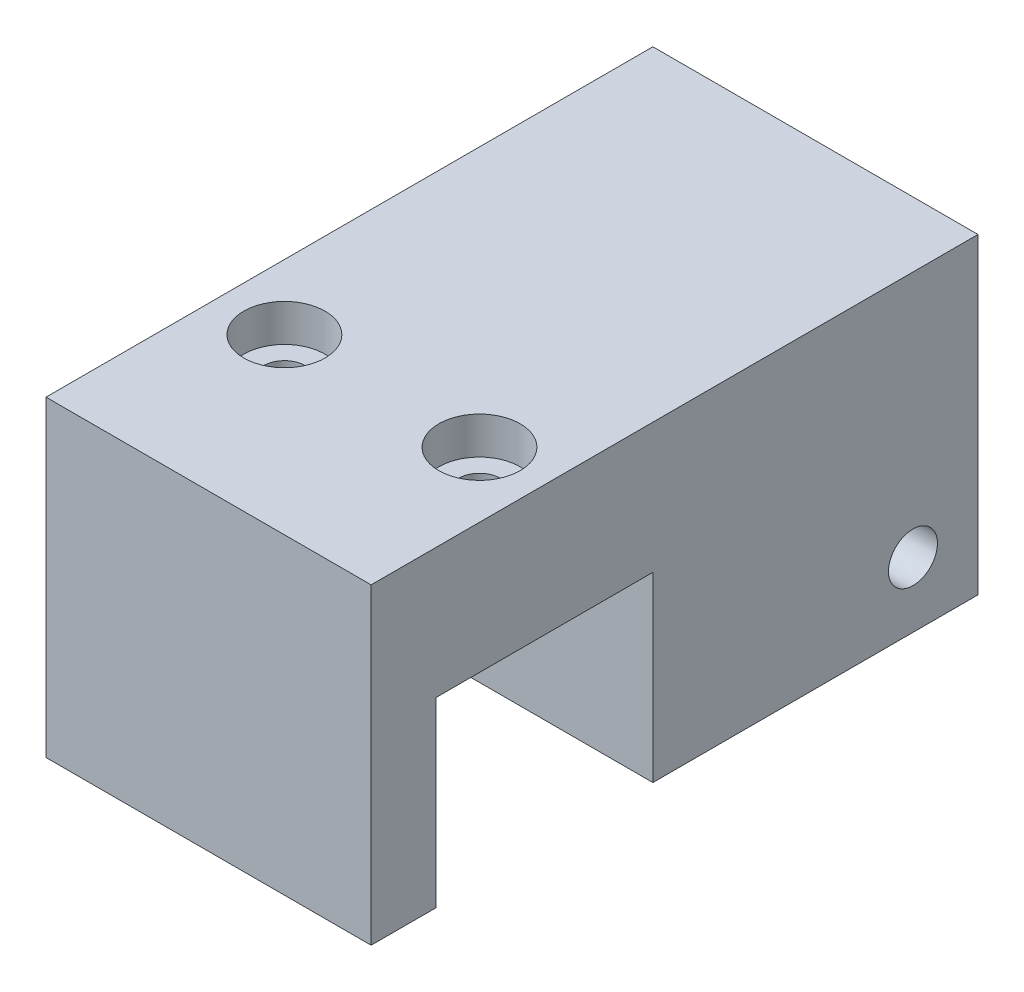
SolidWorks part; units mm, degrees
ref_plane "Front Plane" through (0, 0, 0) normal (0, 0, 1) x (1, 0, 0)
ref_plane "Top Plane" through (0, 0, 0) normal (0, 1, 0) x (1, 0, 0)
ref_plane "Right Plane" through (0, 0, 0) normal (1, 0, 0) x (0, 0, -1)
sketch "Sketch1" plane through (0, 0, 0) normal (1, 0, 0) x (0, 0, -1)
  line L0 (-8.89, 0) -> (-5.08, 0)
  line L1 (0, 0) -> (2.54, 0)
  line L5 (2.54, 0) -> (10.16, 0)
  line L8 (10.16, 0) -> (10.16, 7.62)
  line L9 (0, 0) -> (-8.89, 0)
  line L12 (-8.89, 0) -> (-8.89, 5.08)
  line L14 (-8.89, 0) -> (-8.89, 10.668)
  line L16 (-21.59, 0) -> (-21.59, 10.668)
  line L17 (-25.4, 0) -> (-21.59, 0)
  line L18 (-25.4, 0) -> (-25.4, 18.288)
  line L19 (-25.4, 18.288) -> (-5.08, 18.288)
  line L20 (-5.08, 0) -> (-5.08, 18.288)
  line L21 (-21.59, 10.668) -> (-8.89, 10.668)
  line L23 (10.16, 7.62) -> (10.16, 18.288)
  line L24 (10.16, 18.288) -> (-5.08, 18.288)
  dimension "D5" = 7.62
  dimension "D6" = 8.89
  dimension "D7" = 10.668
  dimension "D9" = 3.81
  dimension "D10" = 3.81
  dimension "D11" = 7.62
  dimension "D12" = 20.32
extrude "Boss-Extrude1" add sketch "Sketch1" along normal blind 19.05
sketch "Sketch4" plane through (0, 18.288, 0) normal (0, 1, 0) x (1, 0, 0)
  line L0 (0, -25.4) -> (0, 10.16) construction
  line L1 (19.05, -25.4) -> (19.05, 10.16) construction
  line L2 (19.05, -25.4) -> (0, -25.4) construction
  point P0 (3.81, -15.24)
  point P1 (15.24, -15.24)
  dimension "D1" = 3.81
  dimension "D2" = 3.81
  dimension "D3" = 10.16
hole_wizard "CBORE for #2 Socket Head Cap Screw1" positions "Sketch14" profile "Sketch15" counterbore size "#2" standard "ANSI Inch" end condition through all
sketch "Sketch14" plane through (0, 18.288, 0) normal (0, 1, 0) x (-1, 0, 0)
  point P0 (-3.81, 15.24)
  point P3 (-15.24, 15.24)
sketch "Sketch15" plane through (3.81, 18.288, 15.24) normal (1, 0, 0) x (0, 0, 1)
  line L0 (0, 0) -> (0, 18.288)
  line L1 (0, 18.288) -> (1.2192, 18.288)
  line L3 (1.2192, 18.288) -> (1.2192, 2.1844)
  line L4 (1.2192, 2.1844) -> (2.3812, 2.1844)
  line L5 (2.3812, 2.1844) -> (2.3812, 0)
  line L7 (2.3812, 0) -> (0, 0)
  line L11 (0, -6.35) -> (0, 107.95) construction
  dimension "Thru Hole Dia." = 2.4384
  dimension "Thru Hole Depth" = 18.288
  dimension "C'Bore Dia." = 4.7625
  dimension "C'Bore Depth" = 2.1844
sketch "Sketch18" plane through (0, 0, 0) normal (-1, 0, 0) x (0, 0, 1)
  line L0 (-10.16, 0) -> (8.89, 0) construction
  line L2 (-10.16, 0) -> (-10.16, 18.288) construction
  point P0 (-6.35, 3.81)
  dimension "D1" = 3.81
  dimension "D2" = 3.81
hole_wizard "#6-40 Tapped Hole2" positions "Sketch19" profile "Sketch20" tap size "#6-40" standard "ANSI Inch" end condition through all
sketch "Sketch19" plane through (0, 0, 0) normal (-1, 0, 0) x (0, 0, 1)
  point P0 (-6.35, 3.81)
sketch "Sketch20" plane through (0, 3.81, -6.35) normal (0, 1, 0) x (0, 0, 1)
  line L0 (0, 0) -> (0, 19.05)
  line L1 (0, 19.05) -> (1.4351, 19.05)
  line L2 (1.4351, 19.05) -> (1.4351, 0)
  line L5 (1.4351, 0) -> (0, 0)
  line L11 (0, -6.35) -> (0, 107.95) construction
  dimension "Thru Tap Drill Dia." = 2.8702
  dimension "Thru Tap Drill Depth" = 19.05
cosmetic thread "Hole Thread1" parameters "D2"=3.5052
